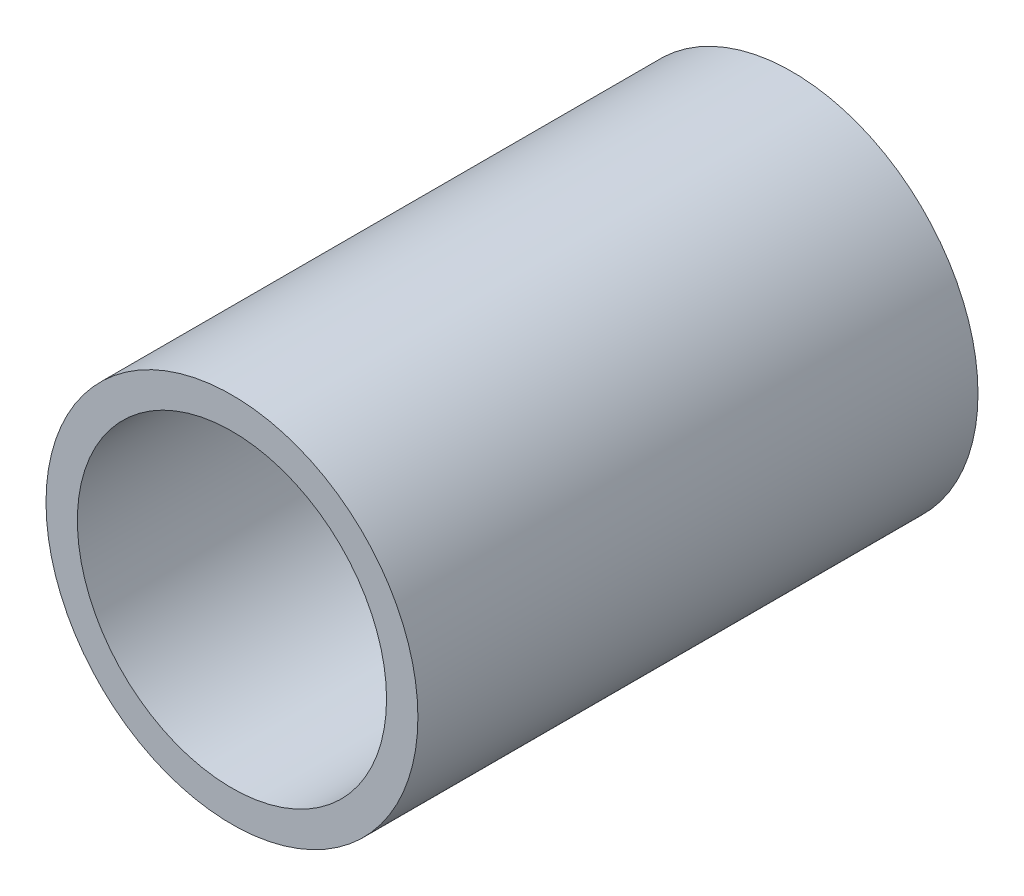
SolidWorks part; units mm, degrees
ref_plane "Front Plane" through (0, 0, 0) normal (0, 0, 1) x (1, 0, 0)
ref_plane "Top Plane" through (0, 0, 0) normal (0, 1, 0) x (1, 0, 0)
ref_plane "Right Plane" through (0, 0, 0) normal (1, 0, 0) x (0, 0, -1)
sketch "Sketch1" plane through (0, 0, 0) normal (0, 0, 1) x (1, 0, 0)
  circle A0 centre (0, 0) radius 21.082
  dimension "Pipe OD" = 42.164
extrude "Extrude-Thin1" add sketch "Sketch1" along normal mid plane 63.5 thin thin type one direction reverse wall 3.556
